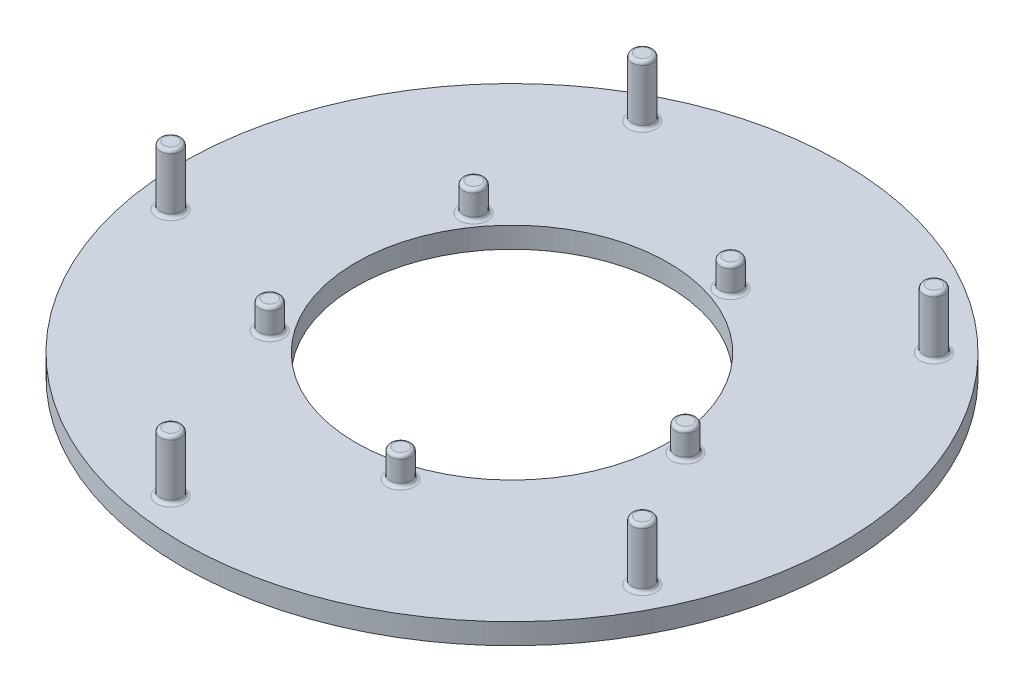
SolidWorks part; units mm, degrees
ref_plane "Front Plane" through (0, 0, 0) normal (0, 0, 1) x (1, 0, 0)
ref_plane "Top Plane" through (0, 0, 0) normal (0, 1, 0) x (1, 0, 0)
ref_plane "Right Plane" through (0, 0, 0) normal (1, 0, 0) x (0, 0, -1)
sketch "Sketch1" plane through (0, 0, 0) normal (0, 1, 0) x (1, 0, 0)
  circle A0 centre (0, 0) radius 22.5
  circle A1 centre (0, 0) radius 47.5
  dimension "D1" = 45
  dimension "D2" = 95
extrude "Boss-Extrude1" add sketch "Sketch1" along normal blind 3
sketch "Sketch2" plane through (0, 3, 0) normal (0, 1, 0) x (1, 0, 0)
  line L0 (-67.5192, 0) -> (70.5599, 0) construction
  line L1 (0, 58.8306) -> (0, -59.2797) construction
  line L2 (0, 0) -> (30.4056, 30.4056) construction
  circle A0 centre (25, 0) radius 1.5
  circle A1 centre (30.4056, 30.4056) radius 1.5
  circle A2 centre (0, 0) radius 25 construction
  circle A3 centre (0, 0) radius 43 construction
  dimension "D1" = 3
  dimension "D2" = 3
  dimension "D3" = 50
  dimension "D4" = 86
  dimension "D5" = 45
extrude "Boss-Extrude2" add sketch "Sketch2" along normal blind 4
fillet "Fillet1" radius 0.5 3 edges at (30.4056, 3, -28.9056) (25, 3, 1.5) (25, 7, 1.5)
sketch "Sketch3" plane through (0, 7, 0) normal (0, 1, 0) x (1, 0, 0)
  circle A0 centre (30.4056, 30.4056) radius 1.5 construction
  circle A1 centre (30.4056, 30.4056) radius 1.5
extrude "Boss-Extrude3" add sketch "Sketch3" along normal blind 4.5
fillet "Fillet2" radius 0.5 1 edges at (30.4056, 11.5, -28.9056)
pattern_circular "CirPattern1" count 5 over 360 about axis through (0, 0, 0) along (0, 1, 0) of "Boss-Extrude2", "Fillet1", "Boss-Extrude3", "Fillet2"
